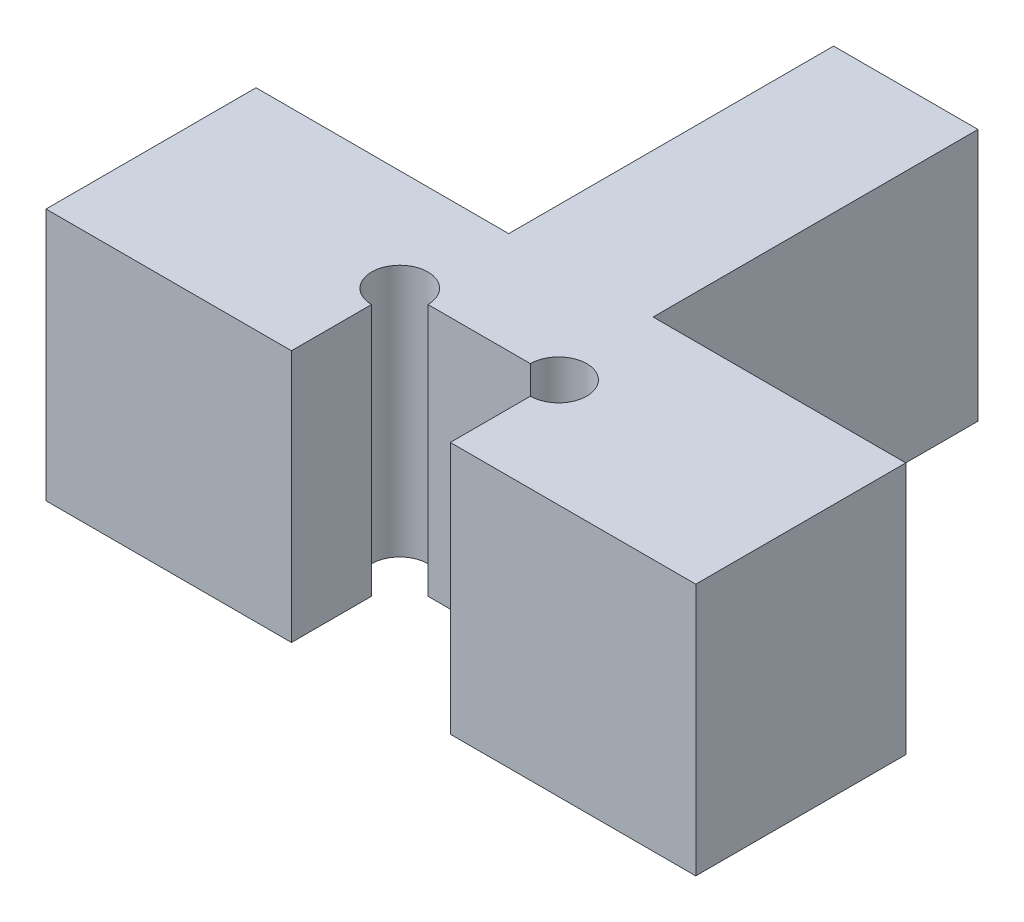
SolidWorks part; units mm, degrees
ref_plane "Front Plane" through (0, 0, 0) normal (0, 0, 1) x (1, 0, 0)
ref_plane "Top Plane" through (0, 0, 0) normal (0, 1, 0) x (1, 0, 0)
ref_plane "Right Plane" through (0, 0, 0) normal (1, 0, 0) x (0, 0, -1)
sketch "Sketch1" plane through (0, 0, 0) normal (0, 1, 0) x (1, 0, 0)
  line L0 (-4.5, -0.1642) -> (-1.1, -0.1642)
  line L1 (4.5, -0.1642) -> (4.5, 2.745)
  line L2 (4.5, 2.745) -> (1, 2.745)
  line L3 (1, 2.745) -> (1, 7.245)
  line L4 (1, 7.245) -> (-1, 7.245)
  line L5 (-1, 7.245) -> (-1, 2.745)
  line L6 (-1, 2.745) -> (-4.5, 2.745)
  line L7 (-4.5, 2.745) -> (-4.5, -0.1642)
  line L8 (1.1, -0.1642) -> (4.5, -0.1642)
  line L9 (-1.1, -0.1642) -> (1.1, -0.1642) construction
  line L10 (-1.1, -0.1642) -> (-1.1, 0.9454)
  line L11 (-0.7096, 1.3358) -> (0.7096, 1.3358)
  line L12 (1.1, -0.1642) -> (1.1, 0.9454)
  line L13 (-1.1, -0.1642) -> (1.1, -0.1642) construction
  line L14 (1, -1.6642) -> (1, 1.2358) construction
  line L15 (-1, 1.2358) -> (1, 1.2358) construction
  line L16 (10.5409, 5.745) -> (-46.7969, 5.745) construction
  line L17 (9.612, 2.745) -> (-45.868, 2.745) construction
  arc A0 (-0.7096, 1.3358) -> (-1.1, 0.9454) centre (-1.1, 1.3358) ccw
  arc A1 (1.1, 0.9454) -> (0.7096, 1.3358) centre (1.1, 1.3358) ccw
  point P4 (0, 0)
  point P25 (0, 7.245)
  dimension "D1" = 0.1
  dimension "D2" = 0.1
  dimension "D3" = 1.5
  dimension "D4" = 1.5
  dimension "D5" = 0.5
  dimension "D6" = 3.5
extrude "Boss-Extrude1" add sketch "Sketch1" along normal blind 3.5 contours L6 L7 L0 L10 A0 L11 A1 L12 L8 L1 L2 L3 L4 L5
